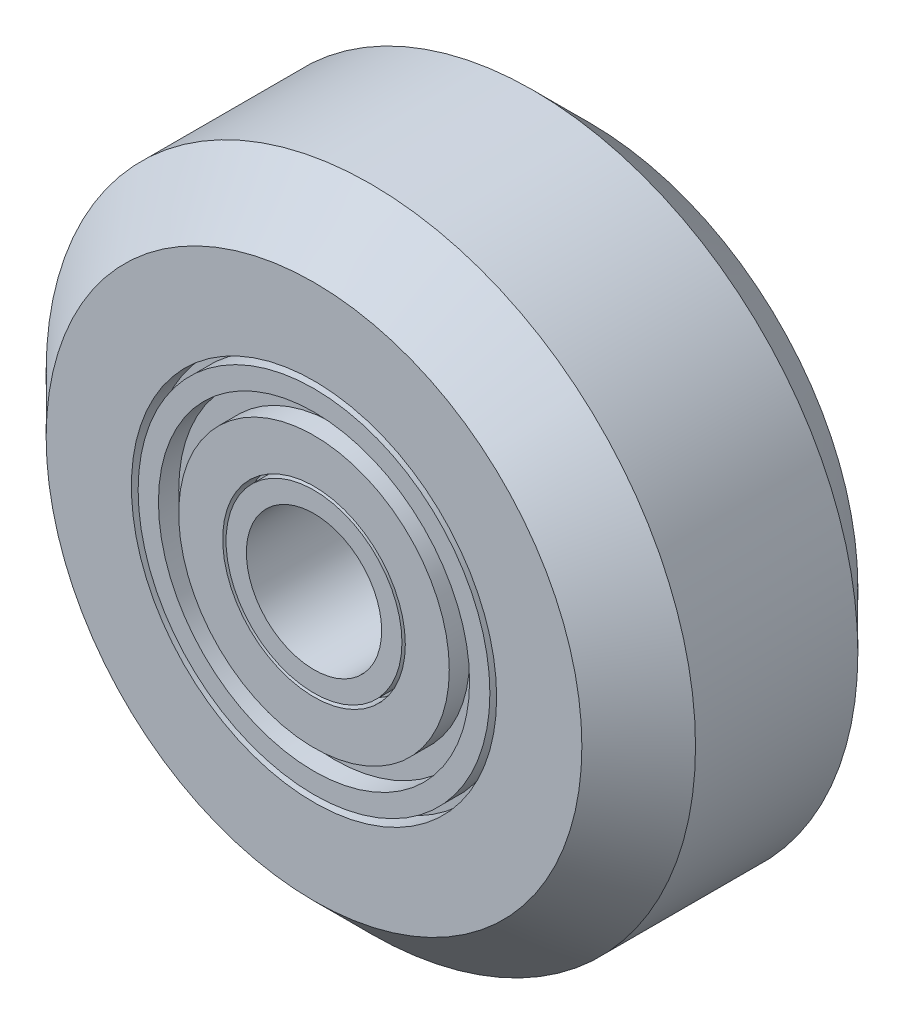
SolidWorks part; units mm, degrees
ref_plane "Front Plane" through (0, 0, 0) normal (0, 0, 1) x (1, 0, 0)
ref_plane "Top Plane" through (0, 0, 0) normal (0, 1, 0) x (1, 0, 0)
ref_plane "Right Plane" through (0, 0, 0) normal (1, 0, 0) x (0, 0, -1)
sketch "Sketch1" plane through (0, 0, 0) normal (0, 0, 1) x (1, 0, 0)
  circle A0 centre (0, 0) radius 12
  dimension "D1" = 24
extrude "Boss-Extrude1" add sketch "Sketch1" along normal mid plane 6
sketch "Sketch3" plane through (0, 0, 3) normal (0, 0, 1) x (1, 0, 0)
  circle A2 centre (0, 0) radius 12
  circle A3 centre (0, 0) radius 12
  dimension "D1" = 0
extrude "Boss-Extrude2" add sketch "Sketch3" along normal blind 2.1 draft 45
sketch "Sketch4" plane through (0, 0, -3) normal (0, 0, -1) x (-1, 0, 0)
  circle A1 centre (0, 0) radius 12
  circle A2 centre (0, 0) radius 12
  dimension "D1" = 0
extrude "Boss-Extrude3" add sketch "Sketch4" along normal blind 2.1 draft 45
sketch "Sketch5" plane through (0, 0, 5.1) normal (0, 0, 1) x (1, 0, 0)
  circle A0 centre (0, 0) radius 2.5
  dimension "D1" = 5
extrude "Cut-Extrude1" cut sketch "Sketch5" against normal through all
sketch "Sketch6" plane through (0, 0, 5.1) normal (0, 0, 1) x (1, 0, 0)
  circle A0 centre (0, 0) radius 3.25
  circle A1 centre (0, 0) radius 5
  circle A2 centre (0, 0) radius 5.75
  circle A3 centre (0, 0) radius 6.5
  circle A4 centre (0, 0) radius 6.75
  circle A5 centre (0, 0) radius 3.375
  dimension "D1" = 6.5
  dimension "D2" = 10
  dimension "D3" = 11.5
  dimension "D4" = 13
  dimension "D5" = 13.5
  dimension "D6" = 6.75
extrude "Cut-Extrude2" cut sketch "Sketch6" against normal blind 0.75 contours A5 A0 | A2 A1 | A4 A3
mirror "Mirror1" about plane through (0, 0, 0) normal (0, 0, 1) of "Cut-Extrude2"
